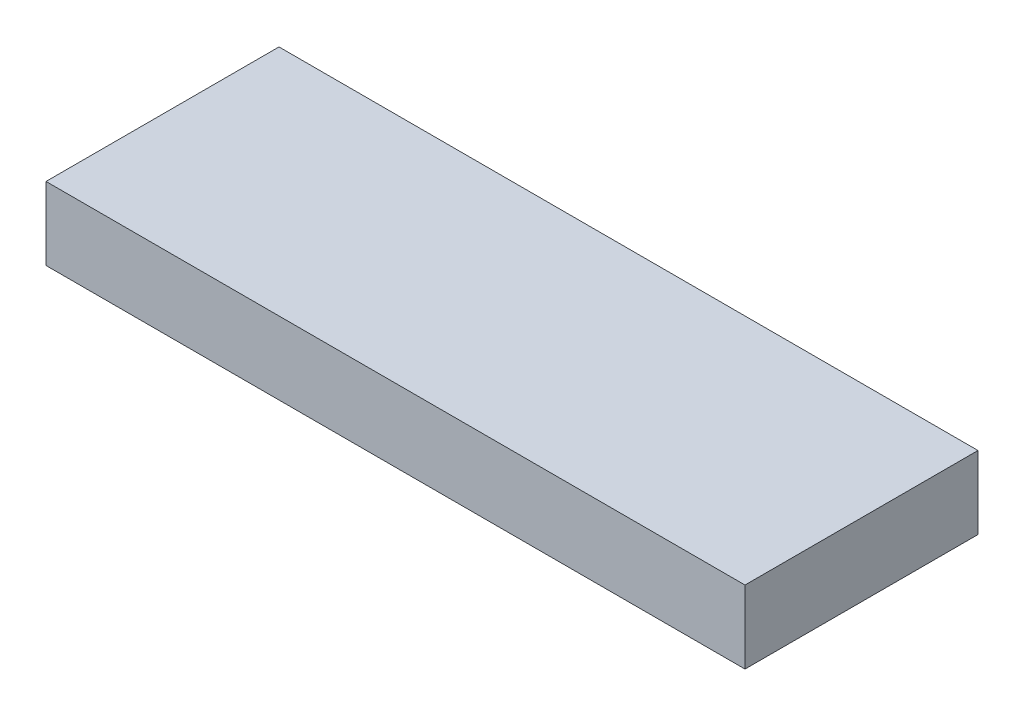
SolidWorks part; units mm, degrees
material "Polyurethane Foam Rigid"
ref_plane "Front Plane" through (0, 0, 0) normal (0, 0, 1) x (1, 0, 0)
ref_plane "Top Plane" through (0, 0, 0) normal (0, 1, 0) x (1, 0, 0)
ref_plane "Right Plane" through (0, 0, 0) normal (1, 0, 0) x (0, 0, -1)
sketch "Sketch1" plane through (0, 0, 0) normal (0, 1, 0) x (1, 0, 0)
  line L1 (-304.8, 101.6) -> (304.8, 101.6)
  line L2 (-304.8, 101.6) -> (-304.8, -101.6)
  line L3 (-304.8, -101.6) -> (304.8, -101.6)
  line L4 (304.8, 101.6) -> (304.8, -101.6)
  point P4 (0, 101.6)
  point P6 (-304.8, 0)
  dimension "D1" = 609.6
  dimension "D2" = 203.2
extrude "Boss-Extrude1" add sketch "Sketch1" along normal mid plane 63.5
